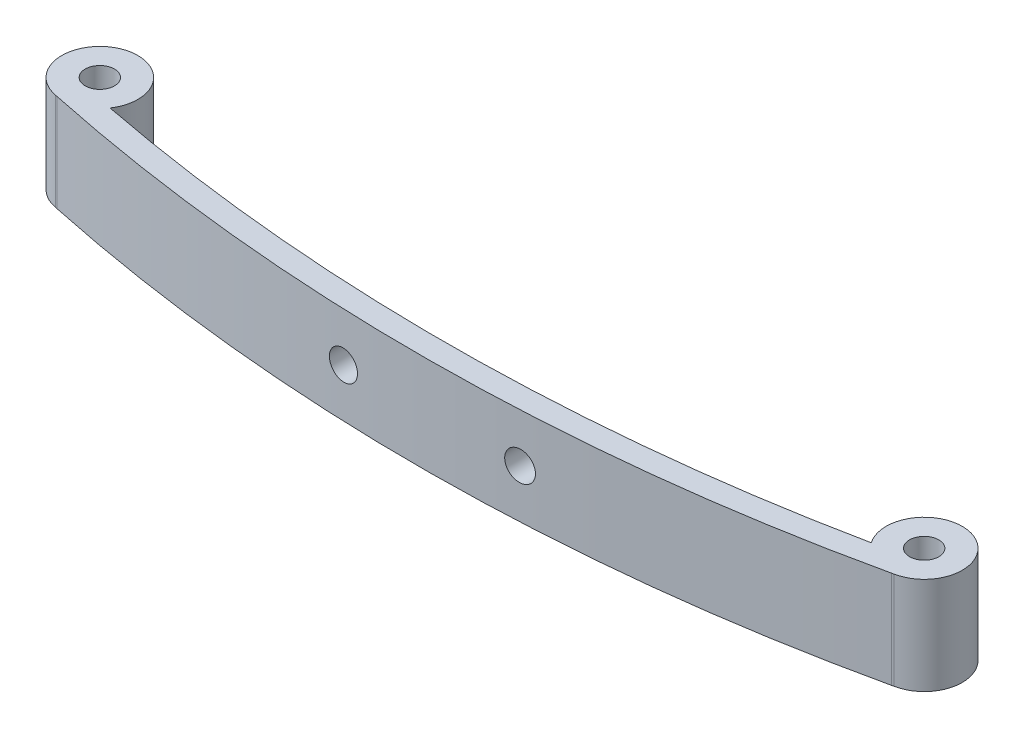
SolidWorks part; units mm, degrees
ref_plane "Front Plane" through (0, 0, 0) normal (0, 0, 1) x (1, 0, 0)
ref_plane "Top Plane" through (0, 0, 0) normal (0, 1, 0) x (1, 0, 0)
ref_plane "Right Plane" through (0, 0, 0) normal (1, 0, 0) x (0, 0, -1)
sketch "Sketch1" plane through (0, 0, 0) normal (0, 1, 0) x (1, 0, 0)
  line L0 (-35, 4.1426) -> (35, 4.5206) construction
  line L1 (35.4342, 1.2875) -> (35.6227, 1.3308)
  line L2 (-35.4132, 0.908) -> (-35.5757, 0.944)
  line L3 (-32.5, 11.9983) -> (-32.5, -12.2817) construction
  line L4 (32.5, 20.0549) -> (32.5, -12.2817) construction
  circle A0 centre (-35, 4.1426) radius 1.25
  circle A1 centre (35, 4.5206) radius 1.25
  arc A2 (-32.3092, 2.3199) -> (-35.5757, 0.944) centre (-35, 4.1426) ccw
  arc A3 (35.6227, 1.3308) -> (32.3291, 2.6689) centre (35, 4.5206) ccw
  arc A4 (-32.3092, 2.3199) -> (32.3291, 2.6689) centre (-0.865, 164.5106) ccw
  arc A5 (-35.4132, 0.908) -> (35.4342, 1.2875) centre (-0.865, 164.5106) ccw
  arc A7 (-35, 2.8648) -> (35, 3.2398) centre (-0.865, 164.5106) ccw construction
  circle A8 centre (-35, 4.1426) radius 3.25 construction
  circle A9 centre (35, 4.5206) radius 3.25 construction
  point P7 (38.108, 5.4708)
  point P18 (-31.892, 5.0928)
  dimension "D1" = 2.5
  dimension "D2" = 2.5
  dimension "D3" = 70
  dimension "D4" = 35
  dimension "D6" = 65
  dimension "D8" = 32.5
  dimension "D5" = 2
  dimension "D7" = 2
extrude "Boss-Extrude1" add sketch "Sketch1" along normal blind 8.3
sketch "Sketch2" plane through (0, 0, 0) normal (0, 0, 1) x (1, 0, 0)
  line L0 (0.0105, 8.3) -> (0, 0) construction
  line L1 (35.4342, 8.3) -> (-35.4132, 8.3) construction
  line L2 (35.6227, 4.15) -> (-35.5757, 4.15) construction
  line L5 (35.6227, 8.3) -> (35.6227, 0) construction
  line L6 (-35.5757, 8.3) -> (-35.5757, 0) construction
  circle A0 centre (7.5052, 4.15) radius 1.25
  circle A1 centre (-7.4948, 4.15) radius 1.25
  point P15 (0.0052, 4.15)
  dimension "D2" = 2.5
  dimension "D3" = 2.5
  dimension "D1" = 15
  dimension "D4" = 7.5
extrude "Cut-Extrude1" cut sketch "Sketch2" against normal through all both and the other way through all
